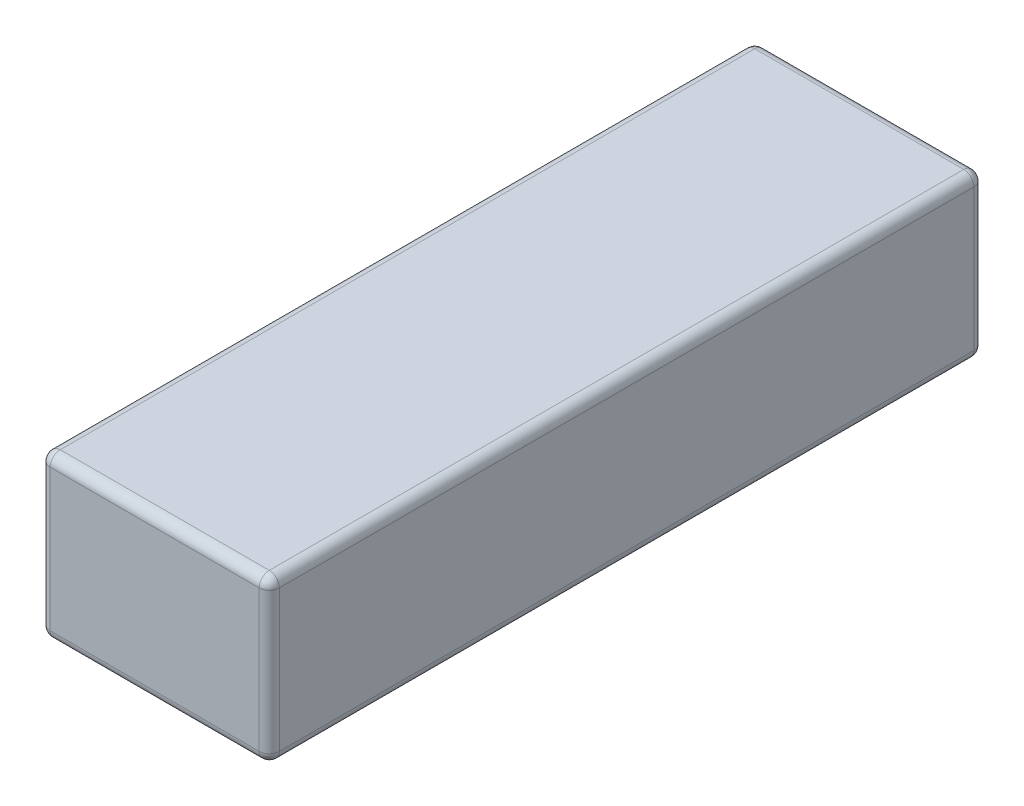
SolidWorks part; units mm, degrees
ref_plane "Alzado" through (0, 0, 0) normal (0, 0, 1) x (1, 0, 0)
ref_plane "Planta" through (0, 0, 0) normal (0, 1, 0) x (1, 0, 0)
ref_plane "Vista lateral" through (0, 0, 0) normal (1, 0, 0) x (0, 0, -1)
sketch "Croquis1" plane through (0, 0, 0) normal (0, 1, 0) x (1, 0, 0)
  line L1 (17, -53) -> (-17, -53)
  line L2 (17, -53) -> (17, 53)
  line L3 (17, 53) -> (-17, 53)
  line L4 (-17, -53) -> (-17, 53)
  line L5 (17, -53) -> (-17, 53) construction
  line L6 (17, 53) -> (-17, -53) construction
  point P0 (0, 0)
  dimension "D1" = 106
  dimension "D2" = 34
extrude "Saliente-Extruir1" add sketch "Croquis1" along normal blind 24
fillet "Redondeo1" radius 1.5 12 edges at (17, 12, -53) (0, 0, -53) (-17, 12, -53) (-17, 12, 53) (-17, 0, 0) (0, 24, -53) (17, 24, 0) (0, 24, 53) (-17, 24, 0) (17, 12, 53) (0, 0, 53) (17, 0, 0)
